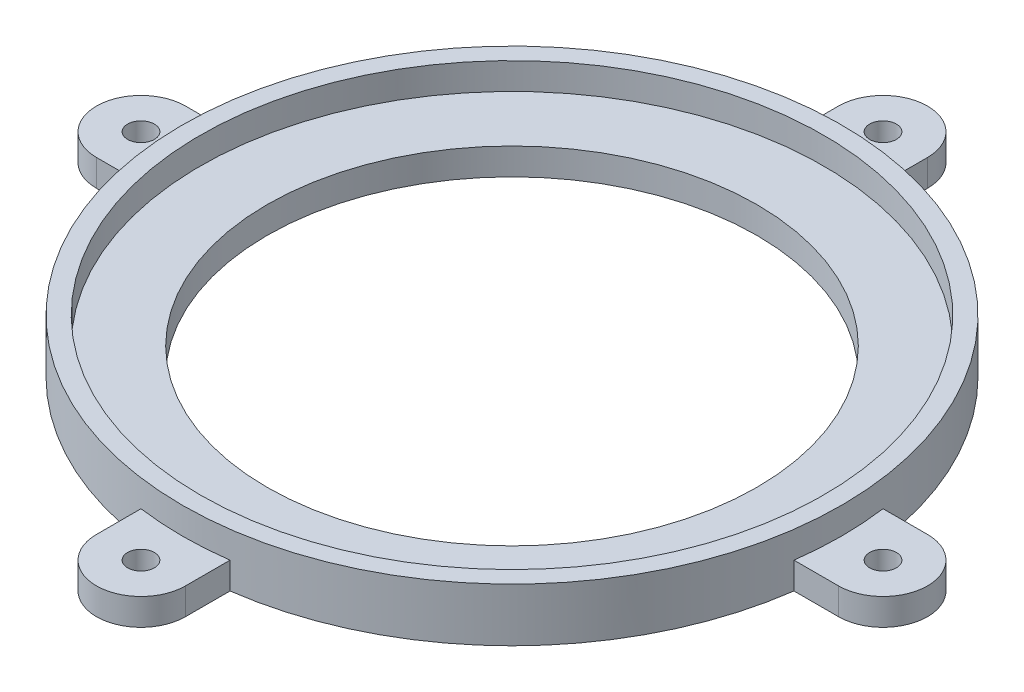
SolidWorks part; units mm, degrees
ref_plane "Front Plane" through (0, 0, 0) normal (0, 0, 1) x (1, 0, 0)
ref_plane "Top Plane" through (0, 0, 0) normal (0, 1, 0) x (1, 0, 0)
ref_plane "Right Plane" through (0, 0, 0) normal (1, 0, 0) x (0, 0, -1)
sketch "Sketch1" plane through (0, 0, 0) normal (0, 1, 0) x (1, 0, 0)
  line L0 (0, -6.35) -> (0, 6.35) construction
  line L1 (0, 6.35) -> (46.559, 6.35) construction
  line L2 (0, -6.35) -> (46.559, -6.35) construction
  line L3 (46.559, 6.35) -> (52.909, 6.35)
  line L4 (46.559, -6.35) -> (52.909, -6.35)
  line L5 (6.35, -46.559) -> (6.35, -52.909)
  line L6 (-6.35, -46.559) -> (-6.35, -52.909)
  line L7 (-46.559, -6.35) -> (-52.909, -6.35)
  line L8 (-46.559, 6.35) -> (-52.909, 6.35)
  line L9 (-6.35, 46.559) -> (-6.35, 52.909)
  line L10 (6.35, 46.559) -> (6.35, 52.909)
  arc A0 (46.559, 6.35) -> (6.35, 46.559) centre (0, 0) ccw
  arc A1 (52.909, 6.35) -> (52.909, -6.35) centre (52.909, 0) cw
  arc A2 (6.35, -52.909) -> (-6.35, -52.909) centre (0, -52.909) cw
  arc A3 (-52.909, -6.35) -> (-52.909, 6.35) centre (-52.909, 0) cw
  arc A4 (-6.35, 52.909) -> (6.35, 52.909) centre (0, 52.909) cw
  arc A5 (-6.35, 46.559) -> (-46.559, 6.35) centre (0, 0) ccw
  arc A6 (-46.559, -6.35) -> (-6.35, -46.559) centre (0, 0) ccw
  arc A7 (6.35, -46.559) -> (46.559, -6.35) centre (0, 0) ccw
  circle A8 centre (52.909, 0) radius 1.905
  circle A9 centre (0, -52.909) radius 1.905
  circle A10 centre (-52.909, 0) radius 1.905
  circle A11 centre (0, 52.909) radius 1.905
  point P5 (0, 0)
  point P29 (0, 0)
  point P36 (0, 0)
  dimension "D1" = 93.98
  dimension "D6" = 3.81
  dimension "D2" = 12.7
  dimension "D3" = 6.35
  dimension "D4" = 6.35
  dimension "D5" = 4
  dimension "D7" = 4
extrude "Boss-Extrude1" add sketch "Sketch1" along normal blind 3.81
sketch "Sketch2" plane through (0, 3.81, 0) normal (0, 1, 0) x (1, 0, 0)
  circle A0 centre (0, 0) radius 34.925
  arc A1 (46.559, 6.35) -> (6.35, 46.559) centre (0, 0) ccw construction
  dimension "D1" = 69.85
extrude "Cut-Extrude2" cut sketch "Sketch2" against normal through all
sketch "Sketch3" plane through (0, 3.81, 0) normal (0, 1, 0) x (1, 0, 0)
  circle A0 centre (0, 0) radius 44.45
  circle A1 centre (0, 0) radius 34.925 construction
  circle A2 centre (0, 0) radius 46.99
  arc A3 (46.559, 6.35) -> (6.35, 46.559) centre (0, 0) ccw construction
  dimension "D1" = 88.9
extrude "Boss-Extrude2" add sketch "Sketch3" along normal blind 3.81
